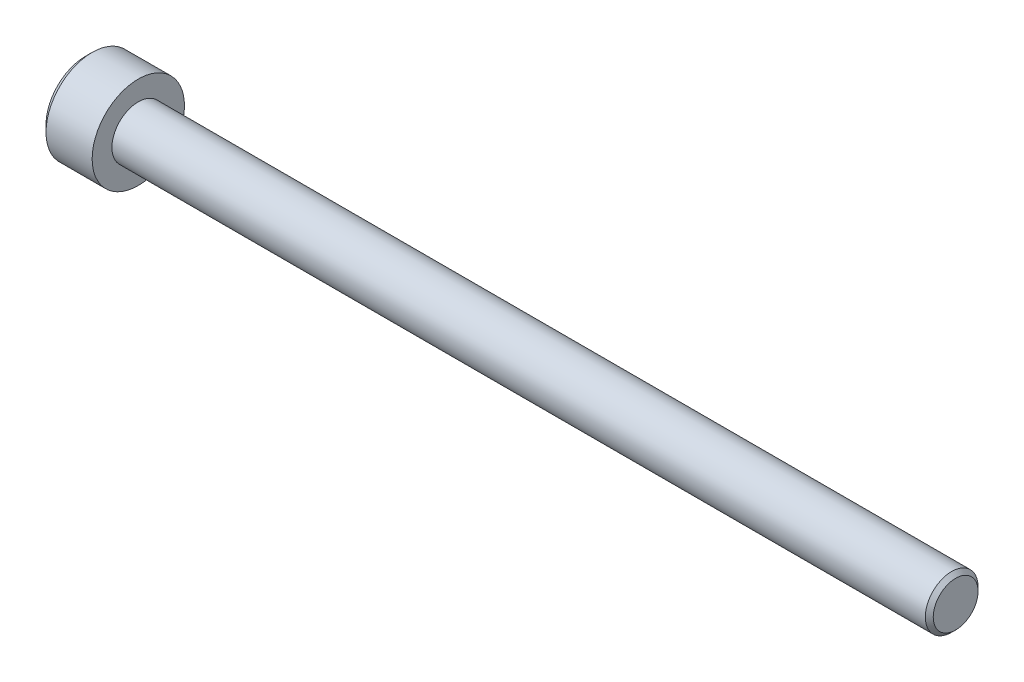
SolidWorks part; units mm, degrees
ref_plane "Front Plane" through (0, 0, 0) normal (0, 0, 1) x (1, 0, 0)
ref_plane "Top Plane" through (0, 0, 0) normal (0, 1, 0) x (1, 0, 0)
ref_plane "Right Plane" through (0, 0, 0) normal (1, 0, 0) x (0, 0, -1)
sketch "Sketch1" plane through (0, 0, 0) normal (0, 0, 1) x (1, 0, 0)
  line L0 (0, 0) -> (66, 0)
  line L1 (0, 0) -> (0, 3.5)
  line L2 (0, 3.5) -> (4, 3.5)
  line L3 (4, 3.5) -> (4, 2)
  line L4 (4, 2) -> (66, 2)
  line L5 (66, 2) -> (66, 0)
  dimension "D1" = 62
  dimension "D2" = 2
  dimension "D3" = 3.5
  dimension "D5" = 4
revolve "Revolve1" add sketch "Sketch1" angle 360 about L0
chamfer "Chamfer1" distance 0.3 angle 45 1 edges at (66, 0, 2)
sketch "Sketch2" plane through (0, 0, 0) normal (-1, 0, 0) x (0, 0, 1)
  line L1 (0, 2) -> (-1.7321, 1)
  line L2 (-1.7321, 1) -> (-1.7321, -1)
  line L3 (-1.7321, -1) -> (0, -2)
  line L4 (0, -2) -> (1.7321, -1)
  line L5 (1.7321, -1) -> (1.7321, 1)
  line L6 (1.7321, 1) -> (0, 2)
  circle A0 centre (0, 0) radius 1.7321 construction
extrude "Cut-Extrude1" cut sketch "Sketch2" against normal blind 1
chamfer "Chamfer2" distance 0.5 angle 45 1 edges at (0, 0, 3.5)
